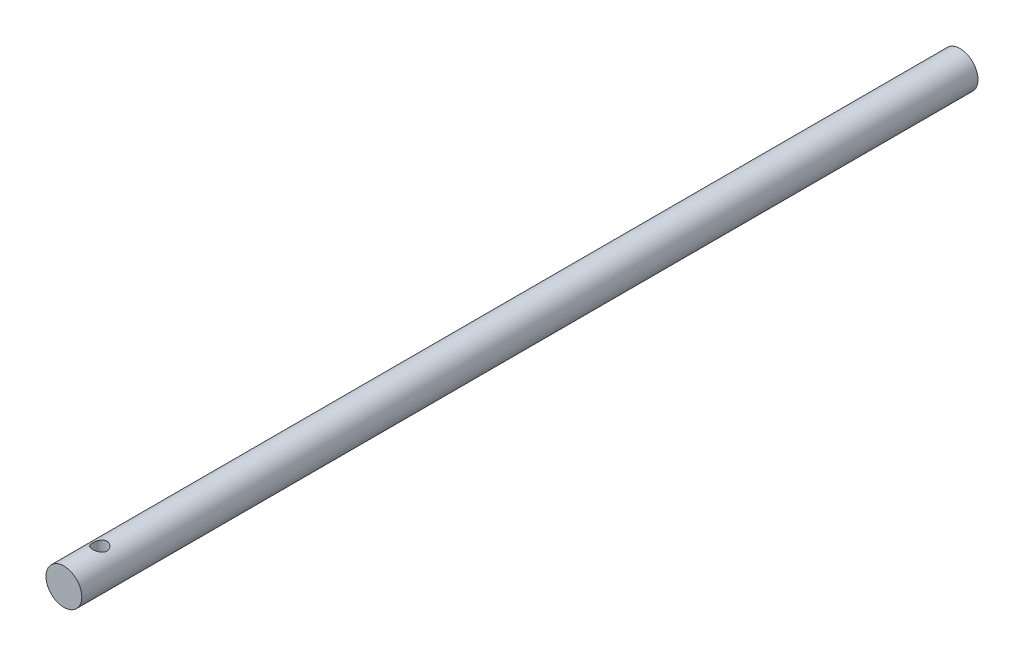
SolidWorks part; units mm, degrees
ref_plane "Plan de face" through (0, 0, 0) normal (0, 0, 1) x (1, 0, 0)
ref_plane "Plan de dessus" through (0, 0, 0) normal (0, 1, 0) x (1, 0, 0)
ref_plane "Plan de droite" through (0, 0, 0) normal (1, 0, 0) x (0, 0, -1)
sketch "Esquisse1" plane through (0, 0, 0) normal (0, 0, 1) x (1, 0, 0)
  circle A0 centre (0, 0) radius 0.5
  dimension "D1" = 1
extrude "Boss.-Extru.1" add sketch "Esquisse1" along normal blind 25 contours A0
sketch "Esquisse3" plane through (0, 0, 0) normal (0, 1, 0) x (1, 0, 0)
  line L0 (0.5, 0) -> (-0.5, 0) construction
  line L1 (-0.5, -25) -> (0.5, -25) construction
  circle A0 centre (0, -1) radius 0.2
  circle A1 centre (0, -24) radius 0.2
  dimension "D2" = 0.4
  dimension "D4" = 0.4
  dimension "D1" = 1
  dimension "D3" = 1
extrude "Enlèv. mat.-Extru.3" cut sketch "Esquisse3" against normal blind 1 contours A0
sketch "Esquisse4" plane through (0, 0, 0) normal (0, 1, 0) x (1, 0, 0)
  line L0 (-0.5, -25) -> (0.5, -25) construction
  circle A0 centre (0, -24) radius 0.2
  dimension "D1" = 0.4
  dimension "D2" = 1
extrude "Enlèv. mat.-Extru.4" cut sketch "Esquisse4" along normal blind 1
